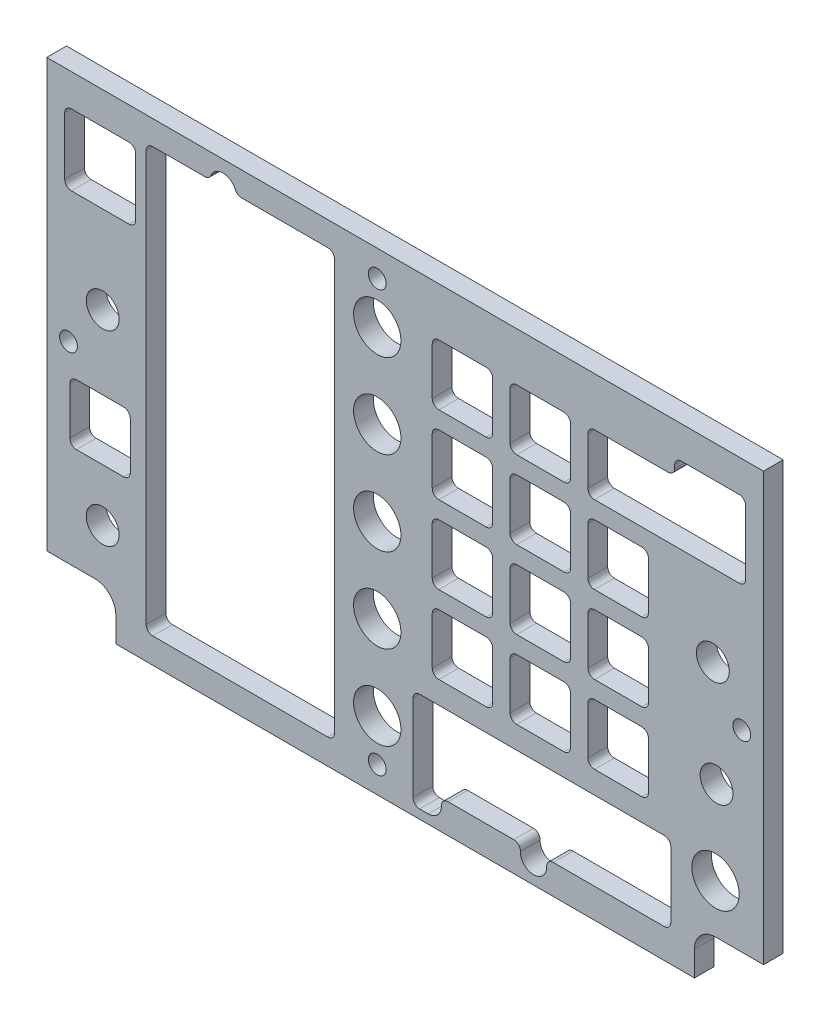
SolidWorks part; units mm, degrees
material "ABS PC"
ref_plane "Front Plane" through (0, 0, 0) normal (0, 0, 1) x (1, 0, 0)
ref_plane "Top Plane" through (0, 0, 0) normal (0, 1, 0) x (1, 0, 0)
ref_plane "Right Plane" through (0, 0, 0) normal (1, 0, 0) x (0, 0, -1)
sketch "Sketch1" plane through (0, 0, 0) normal (0, 0, 1) x (1, 0, 0)
  line L8 (74.93, -171.1167) -> (86.5187, -171.1167)
  line L9 (86.5187, -171.1167) -> (86.5187, -67.9292)
  line L10 (86.5187, -67.9292) -> (-86.5187, -67.9292)
  line L11 (-86.5187, -67.9292) -> (-86.5187, -171.1167)
  line L12 (-86.5187, -171.1167) -> (-74.93, -171.1167)
  line L13 (-69.85, -176.1967) -> (-69.85, -182.2292)
  line L14 (-69.85, -182.2292) -> (69.85, -182.2292)
  line L15 (69.85, -182.2292) -> (69.85, -176.1967)
  line L16 (74.93, -171.1167) -> (86.5187, -171.1167)
  line L17 (86.5187, -171.1167) -> (86.5187, -67.9292)
  line L18 (86.5187, -67.9292) -> (-86.5187, -67.9292)
  line L19 (-86.5187, -67.9292) -> (-86.5187, -171.1167)
  line L20 (-86.5187, -171.1167) -> (-74.93, -171.1167)
  line L21 (-69.85, -176.1967) -> (-69.85, -182.2292)
  line L22 (-69.85, -182.2292) -> (69.85, -182.2292)
  line L23 (69.85, -182.2292) -> (69.85, -176.1967)
  arc A2 (-69.85, -176.1967) -> (-74.93, -171.1167) centre (-74.93, -176.1967) ccw
  arc A3 (74.93, -171.1167) -> (69.85, -176.1967) centre (74.93, -176.1967) ccw
  arc A4 (-69.85, -176.1967) -> (-74.93, -171.1167) centre (-74.93, -176.1967) ccw
  arc A5 (74.93, -171.1167) -> (69.85, -176.1967) centre (74.93, -176.1967) ccw
  dimension "D1" = 0
extrude "Boss-Extrude1" add sketch "Sketch1" against normal blind 4.7625
sketch "Sketch3" plane through (0, 0, 0) normal (0, 0, 1) x (1, 0, 0)
  line L0 (-67.6275, -133.0167) -> (-79.6925, -133.0167) construction
  line L1 (-79.6925, -133.0167) -> (-79.6925, -145.0817) construction
  line L2 (-79.6925, -145.0817) -> (-67.6275, -145.0817) construction
  line L3 (-67.6275, -145.0817) -> (-67.6275, -133.0167) construction
  line L4 (19.8755, -149.3997) -> (19.8755, -137.3347) construction
  line L5 (19.8755, -137.3347) -> (7.8105, -137.3347) construction
  line L6 (7.8105, -137.3347) -> (7.8105, -149.3997) construction
  line L7 (7.8105, -149.3997) -> (19.8755, -149.3997) construction
  line L8 (38.6715, -149.3997) -> (38.6715, -137.3347) construction
  line L9 (38.6715, -137.3347) -> (26.6065, -137.3347) construction
  line L10 (26.6065, -137.3347) -> (26.6065, -149.3997) construction
  line L11 (26.6065, -149.3997) -> (38.6715, -149.3997) construction
  line L12 (45.4025, -149.3997) -> (57.4675, -149.3997) construction
  line L13 (57.4675, -149.3997) -> (57.4675, -137.3347) construction
  line L14 (57.4675, -137.3347) -> (45.4025, -137.3347) construction
  line L15 (45.4025, -137.3347) -> (45.4025, -149.3997) construction
  line L16 (57.4675, -130.6037) -> (57.4675, -118.5387) construction
  line L17 (57.4675, -118.5387) -> (45.4025, -118.5387) construction
  line L18 (45.4025, -118.5387) -> (45.4025, -130.6037) construction
  line L19 (45.4025, -130.6037) -> (57.4675, -130.6037) construction
  line L20 (38.6715, -130.6037) -> (38.6715, -118.5387) construction
  line L21 (38.6715, -118.5387) -> (26.6065, -118.5387) construction
  line L22 (26.6065, -118.5387) -> (26.6065, -130.6037) construction
  line L23 (26.6065, -130.6037) -> (38.6715, -130.6037) construction
  line L24 (19.8755, -130.6037) -> (19.8755, -118.5387) construction
  line L25 (19.8755, -118.5387) -> (7.8105, -118.5387) construction
  line L26 (7.8105, -118.5387) -> (7.8105, -130.6037) construction
  line L27 (7.8105, -130.6037) -> (19.8755, -130.6037) construction
  line L28 (19.8755, -111.8077) -> (19.8755, -99.7427) construction
  line L29 (19.8755, -99.7427) -> (7.8105, -99.7427) construction
  line L30 (7.8105, -99.7427) -> (7.8105, -111.8077) construction
  line L31 (7.8105, -111.8077) -> (19.8755, -111.8077) construction
  line L32 (19.8755, -93.0117) -> (19.8755, -80.9467) construction
  line L33 (19.8755, -80.9467) -> (7.8105, -80.9467) construction
  line L34 (7.8105, -80.9467) -> (7.8105, -93.0117) construction
  line L35 (7.8105, -93.0117) -> (19.8755, -93.0117) construction
  line L36 (38.6715, -93.0117) -> (38.6715, -80.9467) construction
  line L37 (38.6715, -80.9467) -> (26.6065, -80.9467) construction
  line L38 (26.6065, -80.9467) -> (26.6065, -93.0117) construction
  line L39 (26.6065, -93.0117) -> (38.6715, -93.0117) construction
  line L40 (38.6715, -111.8077) -> (38.6715, -99.7427) construction
  line L41 (38.6715, -99.7427) -> (26.6065, -99.7427) construction
  line L42 (26.6065, -99.7427) -> (26.6065, -111.8077) construction
  line L43 (26.6065, -111.8077) -> (38.6715, -111.8077) construction
  line L44 (57.4675, -111.8077) -> (57.4675, -99.7427) construction
  line L45 (57.4675, -99.7427) -> (45.4025, -99.7427) construction
  line L46 (45.4025, -99.7427) -> (45.4025, -111.8077) construction
  line L47 (45.4025, -111.8077) -> (57.4675, -111.8077) construction
  line L48 (57.4675, -93.0117) -> (57.4675, -80.9467) construction
  line L49 (57.4675, -80.9467) -> (45.4025, -80.9467) construction
  line L50 (45.4025, -80.9467) -> (45.4025, -93.0117) construction
  line L51 (45.4025, -93.0117) -> (57.4675, -93.0117) construction
  line L52 (-67.6275, -133.0167) -> (-79.6925, -133.0167)
  line L53 (-79.6925, -133.0167) -> (-79.6925, -145.0817)
  line L54 (-79.6925, -145.0817) -> (-67.6275, -145.0817)
  line L55 (-67.6275, -145.0817) -> (-67.6275, -133.0167)
  line L56 (19.8755, -149.3997) -> (19.8755, -137.3347)
  line L57 (19.8755, -137.3347) -> (7.8105, -137.3347)
  line L58 (7.8105, -137.3347) -> (7.8105, -149.3997)
  line L59 (7.8105, -149.3997) -> (19.8755, -149.3997)
  line L60 (38.6715, -149.3997) -> (38.6715, -137.3347)
  line L61 (38.6715, -137.3347) -> (26.6065, -137.3347)
  line L62 (26.6065, -137.3347) -> (26.6065, -149.3997)
  line L63 (26.6065, -149.3997) -> (38.6715, -149.3997)
  line L64 (45.4025, -149.3997) -> (57.4675, -149.3997)
  line L65 (57.4675, -149.3997) -> (57.4675, -137.3347)
  line L66 (57.4675, -137.3347) -> (45.4025, -137.3347)
  line L67 (45.4025, -137.3347) -> (45.4025, -149.3997)
  line L68 (57.4675, -130.6037) -> (57.4675, -118.5387)
  line L69 (57.4675, -118.5387) -> (45.4025, -118.5387)
  line L70 (45.4025, -118.5387) -> (45.4025, -130.6037)
  line L71 (45.4025, -130.6037) -> (57.4675, -130.6037)
  line L72 (38.6715, -130.6037) -> (38.6715, -118.5387)
  line L73 (38.6715, -118.5387) -> (26.6065, -118.5387)
  line L74 (26.6065, -118.5387) -> (26.6065, -130.6037)
  line L75 (26.6065, -130.6037) -> (38.6715, -130.6037)
  line L76 (19.8755, -130.6037) -> (19.8755, -118.5387)
  line L77 (19.8755, -118.5387) -> (7.8105, -118.5387)
  line L78 (7.8105, -118.5387) -> (7.8105, -130.6037)
  line L79 (7.8105, -130.6037) -> (19.8755, -130.6037)
  line L80 (19.8755, -111.8077) -> (19.8755, -99.7427)
  line L81 (19.8755, -99.7427) -> (7.8105, -99.7427)
  line L82 (7.8105, -99.7427) -> (7.8105, -111.8077)
  line L83 (7.8105, -111.8077) -> (19.8755, -111.8077)
  line L84 (19.8755, -93.0117) -> (19.8755, -80.9467)
  line L85 (19.8755, -80.9467) -> (7.8105, -80.9467)
  line L86 (7.8105, -80.9467) -> (7.8105, -93.0117)
  line L87 (7.8105, -93.0117) -> (19.8755, -93.0117)
  line L88 (38.6715, -93.0117) -> (38.6715, -80.9467)
  line L89 (38.6715, -80.9467) -> (26.6065, -80.9467)
  line L90 (26.6065, -80.9467) -> (26.6065, -93.0117)
  line L91 (26.6065, -93.0117) -> (38.6715, -93.0117)
  line L92 (38.6715, -111.8077) -> (38.6715, -99.7427)
  line L93 (38.6715, -99.7427) -> (26.6065, -99.7427)
  line L94 (26.6065, -99.7427) -> (26.6065, -111.8077)
  line L95 (26.6065, -111.8077) -> (38.6715, -111.8077)
  line L96 (57.4675, -111.8077) -> (57.4675, -99.7427)
  line L97 (57.4675, -99.7427) -> (45.4025, -99.7427)
  line L98 (45.4025, -99.7427) -> (45.4025, -111.8077)
  line L99 (45.4025, -111.8077) -> (57.4675, -111.8077)
  line L100 (57.4675, -93.0117) -> (57.4675, -80.9467)
  line L101 (57.4675, -80.9467) -> (45.4025, -80.9467)
  line L102 (45.4025, -80.9467) -> (45.4025, -93.0117)
  line L103 (45.4025, -93.0117) -> (57.4675, -93.0117)
  circle A0 centre (74.93, -159.3692) radius 4.445 construction
  circle A1 centre (-6.731, -165.7192) radius 4.445 construction
  circle A2 centre (-6.731, -145.3992) radius 4.445 construction
  circle A3 centre (-6.731, -125.0792) radius 4.445 construction
  circle A4 centre (-6.731, -104.7592) radius 4.445 construction
  circle A5 centre (-6.731, -84.4392) radius 4.445 construction
  circle A6 centre (74.93, -159.3692) radius 4.445
  circle A7 centre (-6.731, -165.7192) radius 4.445
  circle A8 centre (-6.731, -145.3992) radius 4.445
  circle A9 centre (-6.731, -125.0792) radius 4.445
  circle A10 centre (-6.731, -104.7592) radius 4.445
  circle A11 centre (-6.731, -84.4392) radius 4.445
extrude "Cut-Extrude1" [suppressed] cut sketch "Sketch3" against normal through all
sketch "Sketch4" plane through (0, 0, 0) normal (0, 0, 1) x (1, 0, 0)
  circle A0 centre (-73.025, -113.9667) radius 3.9688
  circle A1 centre (-73.025, -159.0517) radius 3.9688
  circle A2 centre (74.295, -113.9667) radius 3.9688
  circle A3 centre (75.184, -139.0492) radius 3.9687
  dimension "D1" = 7.9375
extrude "Cut-Extrude2" cut sketch "Sketch4" against normal through all
sketch "Sketch5" plane through (0, 0, 0) normal (0, 0, 1) x (1, 0, 0)
  line L0 (-79.63, -73.9922) -> (-79.63, -94.6322)
  line L1 (-79.63, -94.6322) -> (-67.69, -94.6322)
  line L2 (-67.69, -94.6322) -> (-67.69, -73.9922)
  line L3 (-67.69, -73.9922) -> (-79.63, -73.9922)
  line L4 (-78.36, -75.2622) -> (-78.36, -93.3622)
  line L5 (-78.36, -93.3622) -> (-68.96, -93.3622)
  line L6 (-68.96, -93.3622) -> (-68.96, -75.2622)
  line L7 (-68.96, -75.2622) -> (-78.36, -75.2622)
  line L8 (-78.36, -75.2622) -> (-78.36, -93.3622) construction
  line L9 (-78.36, -93.3622) -> (-68.96, -93.3622) construction
  line L10 (-68.96, -93.3622) -> (-68.96, -75.2622) construction
  line L11 (-68.96, -75.2622) -> (-78.36, -75.2622) construction
  line L12 (68.96, -75.2622) -> (68.96, -93.3622)
  line L13 (68.96, -93.3622) -> (78.36, -93.3622)
  line L14 (78.36, -93.3622) -> (78.36, -75.2622)
  line L15 (78.36, -75.2622) -> (68.96, -75.2622)
  line L16 (68.96, -75.2622) -> (68.96, -93.3622) construction
  line L17 (68.96, -93.3622) -> (78.36, -93.3622) construction
  line L18 (78.36, -93.3622) -> (78.36, -75.2622) construction
  line L19 (78.36, -75.2622) -> (68.96, -75.2622) construction
  line L20 (67.69, -73.9922) -> (67.69, -94.6322)
  line L21 (67.69, -94.6322) -> (79.63, -94.6322)
  line L22 (79.63, -94.6322) -> (79.63, -73.9922)
  line L23 (79.63, -73.9922) -> (67.69, -73.9922)
  line L24 (-61.06, -75.0622) -> (-51.66, -75.0622) construction
  line L25 (-62.53, -73.7922) -> (-17.068, -73.7922)
  line L26 (-62.53, -73.7922) -> (-62.53, -176.1122)
  line L27 (-62.53, -176.1122) -> (-17.068, -176.1122)
  line L28 (-17.068, -73.7922) -> (-17.068, -176.1122)
  line L29 (-62.53, -73.7922) -> (-17.068, -176.1122) construction
  line L30 (-62.53, -176.1122) -> (-17.068, -73.7922) construction
  line L31 (-61.26, -93.3622) -> (-61.26, -75.2622) construction
  line L32 (-51.66, -174.8422) -> (-61.06, -174.8422) construction
  line L33 (-18.338, -167.7344) -> (-18.338, -169.4031) construction
  line L34 (61.52, -158.4422) -> (61.52, -172.5422) construction
  line L35 (5.02, -157.9422) -> (61.02, -157.9422) construction
  line L36 (61.02, -173.0422) -> (5.02, -173.0422) construction
  line L37 (4.52, -172.5422) -> (4.52, -158.4422) construction
  line L38 (61.52, -157.9422) -> (61.52, -173.0422)
  line L39 (4.52, -157.9422) -> (61.52, -157.9422)
  line L40 (61.52, -173.0422) -> (4.52, -173.0422)
  line L41 (4.52, -173.0422) -> (4.52, -157.9422)
  point P20 (-39.799, -124.9522)
  dimension "D4" = 1.27
  dimension "D5" = 1.27
  dimension "D6" = 1.27
  dimension "D7" = 1.27
  dimension "D1" = 0
  dimension "D2" = 0
  dimension "D3" = 1.27
extrude "Cut-Extrude3" [suppressed] cut sketch "Sketch5" against normal through all
sketch "Sketch6" plane through (0, 0, 0) normal (0, 0, 1) x (1, 0, 0)
  line L4 (-67.6275, -133.0167) -> (-79.6925, -133.0167) construction
  line L5 (57.4675, -137.3347) -> (45.4025, -137.3347) construction
  line L6 (45.4025, -137.3347) -> (45.4025, -149.3997) construction
  line L7 (45.4025, -149.3997) -> (57.4675, -149.3997) construction
  line L8 (57.4675, -149.3997) -> (57.4675, -137.3347) construction
  line L9 (45.4025, -130.6037) -> (57.4675, -130.6037) construction
  line L10 (57.4675, -130.6037) -> (57.4675, -118.5387) construction
  line L11 (57.4675, -118.5387) -> (45.4025, -118.5387) construction
  line L12 (45.4025, -118.5387) -> (45.4025, -130.6037) construction
  line L13 (45.4025, -111.8077) -> (57.4675, -111.8077) construction
  line L14 (57.4675, -111.8077) -> (57.4675, -99.7427) construction
  line L15 (57.4675, -99.7427) -> (45.4025, -99.7427) construction
  line L16 (45.4025, -99.7427) -> (45.4025, -111.8077) construction
  line L17 (45.4025, -93.0117) -> (57.4675, -93.0117) construction
  line L18 (57.4675, -93.0117) -> (57.4675, -80.9467) construction
  line L19 (57.4675, -80.9467) -> (45.4025, -80.9467) construction
  line L20 (45.4025, -80.9467) -> (45.4025, -93.0117) construction
  line L21 (26.6065, -149.3997) -> (38.6715, -149.3997) construction
  line L22 (38.6715, -149.3997) -> (38.6715, -137.3347) construction
  line L23 (38.6715, -137.3347) -> (26.6065, -137.3347) construction
  line L24 (26.6065, -137.3347) -> (26.6065, -149.3997) construction
  line L25 (26.6065, -130.6037) -> (38.6715, -130.6037) construction
  line L26 (38.6715, -130.6037) -> (38.6715, -118.5387) construction
  line L27 (38.6715, -118.5387) -> (26.6065, -118.5387) construction
  line L28 (26.6065, -118.5387) -> (26.6065, -130.6037) construction
  line L29 (26.6065, -111.8077) -> (38.6715, -111.8077) construction
  line L30 (38.6715, -111.8077) -> (38.6715, -99.7427) construction
  line L31 (38.6715, -99.7427) -> (26.6065, -99.7427) construction
  line L32 (26.6065, -99.7427) -> (26.6065, -111.8077) construction
  line L33 (26.6065, -93.0117) -> (38.6715, -93.0117) construction
  line L34 (38.6715, -93.0117) -> (38.6715, -80.9467) construction
  line L35 (38.6715, -80.9467) -> (26.6065, -80.9467) construction
  line L36 (26.6065, -80.9467) -> (26.6065, -93.0117) construction
  line L37 (7.8105, -93.0117) -> (19.8755, -93.0117) construction
  line L38 (19.8755, -93.0117) -> (19.8755, -80.9467) construction
  line L39 (19.8755, -80.9467) -> (7.8105, -80.9467) construction
  line L40 (7.8105, -80.9467) -> (7.8105, -93.0117) construction
  line L41 (7.8105, -111.8077) -> (19.8755, -111.8077) construction
  line L42 (19.8755, -111.8077) -> (19.8755, -99.7427) construction
  line L43 (19.8755, -99.7427) -> (7.8105, -99.7427) construction
  line L44 (7.8105, -99.7427) -> (7.8105, -111.8077) construction
  line L45 (19.8755, -118.5387) -> (7.8105, -118.5387) construction
  line L46 (7.8105, -118.5387) -> (7.8105, -130.6037) construction
  line L47 (7.8105, -130.6037) -> (19.8755, -130.6037) construction
  line L48 (19.8755, -130.6037) -> (19.8755, -118.5387) construction
  line L49 (19.8755, -137.3347) -> (7.8105, -137.3347) construction
  line L50 (7.8105, -137.3347) -> (7.8105, -149.3997) construction
  line L51 (7.8105, -149.3997) -> (19.8755, -149.3997) construction
  line L52 (19.8755, -149.3997) -> (19.8755, -137.3347) construction
  line L53 (-79.6925, -133.0167) -> (-79.6925, -145.0817) construction
  line L54 (-79.6925, -145.0817) -> (-67.6275, -145.0817) construction
  line L55 (-67.6275, -145.0817) -> (-67.6275, -133.0167) construction
  line L56 (57.4675, -137.3347) -> (45.4025, -137.3347) construction
  line L57 (45.4025, -137.3347) -> (45.4025, -149.3997) construction
  line L58 (45.4025, -149.3997) -> (57.4675, -149.3997) construction
  line L59 (57.4675, -149.3997) -> (57.4675, -137.3347) construction
  line L60 (45.4025, -130.6037) -> (57.4675, -130.6037) construction
  line L61 (57.4675, -130.6037) -> (57.4675, -118.5387) construction
  line L62 (57.4675, -118.5387) -> (45.4025, -118.5387) construction
  line L63 (45.4025, -118.5387) -> (45.4025, -130.6037) construction
  line L64 (45.4025, -111.8077) -> (57.4675, -111.8077) construction
  line L65 (57.4675, -111.8077) -> (57.4675, -99.7427) construction
  line L66 (57.4675, -99.7427) -> (45.4025, -99.7427) construction
  line L67 (45.4025, -99.7427) -> (45.4025, -111.8077) construction
  line L68 (45.4025, -93.0117) -> (57.4675, -93.0117) construction
  line L69 (57.4675, -93.0117) -> (57.4675, -80.9467) construction
  line L70 (57.4675, -80.9467) -> (45.4025, -80.9467) construction
  line L71 (45.4025, -80.9467) -> (45.4025, -93.0117) construction
  line L72 (26.6065, -149.3997) -> (38.6715, -149.3997) construction
  line L73 (38.6715, -149.3997) -> (38.6715, -137.3347) construction
  line L74 (38.6715, -137.3347) -> (26.6065, -137.3347) construction
  line L75 (26.6065, -137.3347) -> (26.6065, -149.3997) construction
  line L76 (26.6065, -130.6037) -> (38.6715, -130.6037) construction
  line L77 (38.6715, -130.6037) -> (38.6715, -118.5387) construction
  line L78 (38.6715, -118.5387) -> (26.6065, -118.5387) construction
  line L79 (26.6065, -118.5387) -> (26.6065, -130.6037) construction
  line L80 (26.6065, -111.8077) -> (38.6715, -111.8077) construction
  line L81 (38.6715, -111.8077) -> (38.6715, -99.7427) construction
  line L82 (38.6715, -99.7427) -> (26.6065, -99.7427) construction
  line L83 (26.6065, -99.7427) -> (26.6065, -111.8077) construction
  line L84 (26.6065, -93.0117) -> (38.6715, -93.0117) construction
  line L85 (38.6715, -93.0117) -> (38.6715, -80.9467) construction
  line L86 (38.6715, -80.9467) -> (26.6065, -80.9467) construction
  line L87 (26.6065, -80.9467) -> (26.6065, -93.0117) construction
  line L88 (7.8105, -93.0117) -> (19.8755, -93.0117) construction
  line L89 (19.8755, -93.0117) -> (19.8755, -80.9467) construction
  line L90 (19.8755, -80.9467) -> (7.8105, -80.9467) construction
  line L91 (7.8105, -80.9467) -> (7.8105, -93.0117) construction
  line L92 (7.8105, -111.8077) -> (19.8755, -111.8077) construction
  line L93 (19.8755, -111.8077) -> (19.8755, -99.7427) construction
  line L94 (19.8755, -99.7427) -> (7.8105, -99.7427) construction
  line L95 (7.8105, -99.7427) -> (7.8105, -111.8077) construction
  line L96 (19.8755, -118.5387) -> (7.8105, -118.5387) construction
  line L97 (7.8105, -118.5387) -> (7.8105, -130.6037) construction
  line L98 (7.8105, -130.6037) -> (19.8755, -130.6037) construction
  line L99 (19.8755, -130.6037) -> (19.8755, -118.5387) construction
  line L100 (19.8755, -137.3347) -> (7.8105, -137.3347) construction
  line L101 (7.8105, -137.3347) -> (7.8105, -149.3997) construction
  line L102 (7.8105, -149.3997) -> (19.8755, -149.3997) construction
  line L103 (19.8755, -149.3997) -> (19.8755, -137.3347) construction
  line L104 (-67.6275, -133.0167) -> (-79.6925, -133.0167) construction
  line L105 (-79.6925, -133.0167) -> (-79.6925, -145.0817) construction
  line L106 (-79.6925, -145.0817) -> (-67.6275, -145.0817) construction
  line L107 (-67.6275, -145.0817) -> (-67.6275, -133.0167) construction
  line L108 (58.7375, -136.0647) -> (44.1325, -136.0647)
  line L109 (44.1325, -136.0647) -> (44.1325, -150.6697)
  line L110 (44.1325, -150.6697) -> (58.7375, -150.6697)
  line L111 (58.7375, -150.6697) -> (58.7375, -136.0647)
  line L112 (44.1325, -131.8737) -> (58.7375, -131.8737)
  line L113 (58.7375, -131.8737) -> (58.7375, -117.2687)
  line L114 (58.7375, -117.2687) -> (44.1325, -117.2687)
  line L115 (44.1325, -117.2687) -> (44.1325, -131.8737)
  line L116 (44.1325, -113.0777) -> (58.7375, -113.0777)
  line L117 (58.7375, -113.0777) -> (58.7375, -98.4727)
  line L118 (58.7375, -98.4727) -> (44.1325, -98.4727)
  line L119 (44.1325, -98.4727) -> (44.1325, -113.0777)
  line L120 (44.1325, -94.2817) -> (58.7375, -94.2817)
  line L121 (58.7375, -94.2817) -> (58.7375, -79.6767)
  line L122 (58.7375, -79.6767) -> (44.1325, -79.6767)
  line L123 (44.1325, -79.6767) -> (44.1325, -94.2817)
  line L124 (25.3365, -150.6697) -> (39.9415, -150.6697)
  line L125 (39.9415, -150.6697) -> (39.9415, -136.0647)
  line L126 (39.9415, -136.0647) -> (25.3365, -136.0647)
  line L127 (25.3365, -136.0647) -> (25.3365, -150.6697)
  line L128 (25.3365, -131.8737) -> (39.9415, -131.8737)
  line L129 (39.9415, -131.8737) -> (39.9415, -117.2687)
  line L130 (39.9415, -117.2687) -> (25.3365, -117.2687)
  line L131 (25.3365, -117.2687) -> (25.3365, -131.8737)
  line L132 (25.3365, -113.0777) -> (39.9415, -113.0777)
  line L133 (39.9415, -113.0777) -> (39.9415, -98.4727)
  line L134 (39.9415, -98.4727) -> (25.3365, -98.4727)
  line L135 (25.3365, -98.4727) -> (25.3365, -113.0777)
  line L136 (25.3365, -94.2817) -> (39.9415, -94.2817)
  line L137 (39.9415, -94.2817) -> (39.9415, -79.6767)
  line L138 (39.9415, -79.6767) -> (25.3365, -79.6767)
  line L139 (25.3365, -79.6767) -> (25.3365, -94.2817)
  line L140 (6.5405, -94.2817) -> (21.1455, -94.2817)
  line L141 (21.1455, -94.2817) -> (21.1455, -79.6767)
  line L142 (21.1455, -79.6767) -> (6.5405, -79.6767)
  line L143 (6.5405, -79.6767) -> (6.5405, -94.2817)
  line L144 (6.5405, -113.0777) -> (21.1455, -113.0777)
  line L145 (21.1455, -113.0777) -> (21.1455, -98.4727)
  line L146 (21.1455, -98.4727) -> (6.5405, -98.4727)
  line L147 (6.5405, -98.4727) -> (6.5405, -113.0777)
  line L148 (21.1455, -117.2687) -> (6.5405, -117.2687)
  line L149 (6.5405, -117.2687) -> (6.5405, -131.8737)
  line L150 (6.5405, -131.8737) -> (21.1455, -131.8737)
  line L151 (21.1455, -131.8737) -> (21.1455, -117.2687)
  line L152 (21.1455, -136.0647) -> (6.5405, -136.0647)
  line L153 (6.5405, -136.0647) -> (6.5405, -150.6697)
  line L154 (6.5405, -150.6697) -> (21.1455, -150.6697)
  line L155 (21.1455, -150.6697) -> (21.1455, -136.0647)
  line L156 (-66.3575, -131.7467) -> (-80.9625, -131.7467)
  line L157 (-80.9625, -131.7467) -> (-80.9625, -146.3517)
  line L158 (-80.9625, -146.3517) -> (-66.3575, -146.3517)
  line L159 (-66.3575, -146.3517) -> (-66.3575, -131.7467)
  circle A6 centre (74.93, -159.3692) radius 4.445 construction
  circle A7 centre (-6.731, -165.7192) radius 4.445 construction
  circle A9 centre (-6.731, -145.3992) radius 4.445 construction
  circle A12 centre (-6.731, -125.0792) radius 4.445 construction
  circle A16 centre (-6.731, -104.7592) radius 4.445 construction
  circle A21 centre (-6.731, -84.4392) radius 4.445 construction
  circle A33 centre (74.93, -159.3692) radius 4.445 construction
  circle A34 centre (-6.731, -165.7192) radius 4.445 construction
  circle A35 centre (-6.731, -145.3992) radius 4.445 construction
  circle A36 centre (-6.731, -125.0792) radius 4.445 construction
  circle A37 centre (-6.731, -104.7592) radius 4.445 construction
  circle A38 centre (-6.731, -84.4392) radius 4.445 construction
  circle A39 centre (74.93, -159.3692) radius 5.715
  circle A40 centre (-6.731, -165.7192) radius 5.715
  circle A41 centre (-6.731, -145.3992) radius 5.715
  circle A42 centre (-6.731, -125.0792) radius 5.715
  circle A43 centre (-6.731, -104.7592) radius 5.715
  circle A44 centre (-6.731, -84.4392) radius 5.715
  dimension "D1" = 1.27
extrude "Cut-Extrude4" [suppressed] cut sketch "Sketch6" against normal through all
sketch "Sketch7" plane through (0, 0, 0) normal (0, 0, 1) x (1, 0, 0)
  line L0 (66.04, -176.9122) -> (66.04, -148.2722)
  line L1 (66.04, -148.2722) -> (0, -148.2722)
  line L2 (0, -148.2722) -> (0, -176.9122)
  line L3 (0, -176.9122) -> (66.04, -176.9122)
  line L4 (64.77, -175.6422) -> (64.77, -149.5422)
  line L5 (64.77, -149.5422) -> (1.27, -149.5422)
  line L6 (1.27, -149.5422) -> (1.27, -175.6422)
  line L7 (1.27, -175.6422) -> (64.77, -175.6422)
  line L8 (64.77, -175.6422) -> (64.77, -149.5422) construction
  line L9 (64.77, -149.5422) -> (1.27, -149.5422) construction
  line L10 (1.27, -149.5422) -> (1.27, -175.6422) construction
  line L11 (1.27, -175.6422) -> (64.77, -175.6422) construction
  dimension "D1" = 0
  dimension "D2" = 1.27
extrude "Cut-Extrude5" [suppressed] cut sketch "Sketch7" against normal through all
hole_wizard "#6 Clearance Hole2" positions "Sketch10" profile "Sketch11" hole size "#6" standard "ANSI Inch" end condition through all
sketch "Sketch10" plane through (0, 0, 1.5875) normal (0, 0, 1) x (-1, 0, 0)
  point P0 (-81.28, 124.6982)
  point P3 (6.731, 175.8792)
  point P6 (81.28, 124.6982)
  point P9 (6.731, 74.2792)
sketch "Sketch11" plane through (81.28, -124.6982, 1.5875) normal (1, 0, 0) x (0, -1, 0)
  line L0 (0, 0) -> (0, 6.35)
  line L1 (0, 6.35) -> (2.1526, 6.35)
  line L2 (2.1526, 6.35) -> (2.1526, 0)
  line L3 (2.1526, 0) -> (0, 0)
  line L4 (0, -6.35) -> (0, 107.95) construction
  dimension "Thru Hole Dia." = 4.3053
  dimension "Thru Hole Depth" = 6.35
sketch "Sketch12" plane through (0, 0, -4.7625) normal (0, 0, -1) x (-1, 0, 0)
  line L0 (73.6125, -76.7792) -> (73.6125, -91.7792) construction
  line L1 (-73.6482, -76.8365) -> (-73.6482, -91.8365) construction
  line L4 (66.1125, -76.7792) -> (66.1125, -91.7792)
  line L5 (81.1125, -76.7792) -> (66.1125, -76.7792)
  line L6 (66.1125, -91.7792) -> (81.1125, -91.7792)
  line L7 (81.1125, -91.7792) -> (81.1125, -76.7792)
  line L10 (-81.1482, -76.8365) -> (-81.1482, -91.8365)
  line L11 (-66.1482, -91.8365) -> (-66.1482, -76.8365)
  line L12 (-66.1482, -91.8365) -> (-81.1482, -91.8365)
  line L13 (-81.1482, -76.8365) -> (-66.1482, -76.8365)
  point P12 (-73.6482, -84.3365)
  point P13 (73.6125, -84.2792)
  dimension "D1" = 15
extrude "Cut-Extrude6" [suppressed] cut sketch "Sketch12" against normal up to next
sketch "Sketch15" plane through (0, 0, -4.7625) normal (0, 0, -1) x (-1, 0, 0)
  line L4 (-58.7375, -137.6522) -> (-58.7375, -149.0822)
  line L5 (-45.72, -136.0647) -> (-57.15, -136.0647)
  line L6 (-44.1325, -149.0822) -> (-44.1325, -137.6522)
  line L7 (-57.15, -150.6697) -> (-45.72, -150.6697)
  line L8 (-58.7375, -137.6522) -> (-58.7375, -149.0822)
  line L9 (-45.72, -136.0647) -> (-57.15, -136.0647)
  line L10 (-44.1325, -149.0822) -> (-44.1325, -137.6522)
  line L11 (-57.15, -150.6697) -> (-45.72, -150.6697)
  line L12 (-58.7375, -118.8562) -> (-58.7375, -130.2862)
  line L13 (-45.72, -117.2687) -> (-57.15, -117.2687)
  line L14 (-44.1325, -130.2862) -> (-44.1325, -118.8562)
  line L15 (-57.15, -131.8737) -> (-45.72, -131.8737)
  line L16 (-58.7375, -118.8562) -> (-58.7375, -130.2862)
  line L17 (-45.72, -117.2687) -> (-57.15, -117.2687)
  line L18 (-44.1325, -130.2862) -> (-44.1325, -118.8562)
  line L19 (-57.15, -131.8737) -> (-45.72, -131.8737)
  line L20 (-58.7375, -100.0602) -> (-58.7375, -111.4902)
  line L21 (-45.72, -98.4727) -> (-57.15, -98.4727)
  line L22 (-44.1325, -111.4902) -> (-44.1325, -100.0602)
  line L23 (-57.15, -113.0777) -> (-45.72, -113.0777)
  line L24 (-58.7375, -100.0602) -> (-58.7375, -111.4902)
  line L25 (-45.72, -98.4727) -> (-57.15, -98.4727)
  line L26 (-44.1325, -111.4902) -> (-44.1325, -100.0602)
  line L27 (-57.15, -113.0777) -> (-45.72, -113.0777)
  line L28 (-39.9415, -81.2642) -> (-39.9415, -92.6942)
  line L29 (-45.72, -79.6767) -> (-63.4882, -79.6767)
  line L30 (-44.1325, -92.6942) -> (-44.1325, -81.2642)
  line L31 (-80.6332, -94.2817) -> (-45.72, -94.2817)
  line L32 (-82.2207, -77.3272) -> (-82.2207, -92.6942)
  line L33 (-66.6632, -75.7397) -> (-80.6332, -75.7397)
  line L34 (-45.72, -79.6767) -> (-63.4882, -79.6767)
  line L35 (-44.1325, -92.6942) -> (-44.1325, -81.2642)
  line L36 (-80.6332, -94.2817) -> (-45.72, -94.2817)
  line L37 (-82.2207, -77.3272) -> (-82.2207, -92.6942)
  line L38 (-66.6632, -75.7397) -> (-80.6332, -75.7397)
  line L39 (-26.924, -79.6767) -> (-38.354, -79.6767)
  line L40 (-25.3365, -92.6942) -> (-25.3365, -81.2642)
  line L41 (-38.354, -94.2817) -> (-26.924, -94.2817)
  line L42 (-39.9415, -81.2642) -> (-39.9415, -92.6942)
  line L43 (-26.924, -79.6767) -> (-38.354, -79.6767)
  line L44 (-25.3365, -92.6942) -> (-25.3365, -81.2642)
  line L45 (-38.354, -94.2817) -> (-26.924, -94.2817)
  line L46 (-39.9415, -100.0602) -> (-39.9415, -111.4902)
  line L47 (-26.924, -98.4727) -> (-38.354, -98.4727)
  line L48 (-25.3365, -111.4902) -> (-25.3365, -100.0602)
  line L49 (-38.354, -113.0777) -> (-26.924, -113.0777)
  line L50 (-39.9415, -100.0602) -> (-39.9415, -111.4902)
  line L51 (-26.924, -98.4727) -> (-38.354, -98.4727)
  line L52 (-25.3365, -111.4902) -> (-25.3365, -100.0602)
  line L53 (-38.354, -113.0777) -> (-26.924, -113.0777)
  line L54 (-39.9415, -118.8562) -> (-39.9415, -130.2862)
  line L55 (-26.924, -117.2687) -> (-38.354, -117.2687)
  line L56 (-25.3365, -130.2862) -> (-25.3365, -118.8562)
  line L57 (-38.354, -131.8737) -> (-26.924, -131.8737)
  line L58 (-39.9415, -118.8562) -> (-39.9415, -130.2862)
  line L59 (-26.924, -117.2687) -> (-38.354, -117.2687)
  line L60 (-25.3365, -130.2862) -> (-25.3365, -118.8562)
  line L61 (-38.354, -131.8737) -> (-26.924, -131.8737)
  line L62 (-39.9415, -137.6522) -> (-39.9415, -149.0822)
  line L63 (-26.924, -136.0647) -> (-38.354, -136.0647)
  line L64 (-25.3365, -149.0822) -> (-25.3365, -137.6522)
  line L65 (-38.354, -150.6697) -> (-26.924, -150.6697)
  line L66 (-39.9415, -137.6522) -> (-39.9415, -149.0822)
  line L67 (-26.924, -136.0647) -> (-38.354, -136.0647)
  line L68 (-25.3365, -149.0822) -> (-25.3365, -137.6522)
  line L69 (-38.354, -150.6697) -> (-26.924, -150.6697)
  line L70 (-6.5405, -149.0822) -> (-6.5405, -137.6522)
  line L71 (-19.558, -150.6697) -> (-8.128, -150.6697)
  line L72 (-26.2305, -175.1172) -> (-10.3495, -175.1172)
  line L73 (-62.5475, -175.1172) -> (-35.7495, -175.1172)
  line L74 (-64.135, -157.6547) -> (-64.135, -173.5297)
  line L75 (-3.4925, -156.0672) -> (-62.5475, -156.0672)
  line L76 (-1.905, -178.4617) -> (-1.905, -157.6547)
  line L77 (-5.59, -180.0492) -> (-3.4925, -180.0492)
  line L78 (-26.2305, -175.1172) -> (-10.3495, -175.1172)
  line L79 (-62.5475, -175.1172) -> (-35.7495, -175.1172)
  line L80 (-64.135, -157.6547) -> (-64.135, -173.5297)
  line L81 (-3.4925, -156.0672) -> (-62.5475, -156.0672)
  line L82 (-1.905, -178.4617) -> (-1.905, -157.6547)
  line L83 (-5.59, -180.0492) -> (-3.4925, -180.0492)
  line L84 (-21.1455, -137.6522) -> (-21.1455, -149.0822)
  line L85 (-8.128, -136.0647) -> (-19.558, -136.0647)
  line L86 (-6.5405, -149.0822) -> (-6.5405, -137.6522)
  line L87 (-19.558, -150.6697) -> (-8.128, -150.6697)
  line L88 (-21.1455, -137.6522) -> (-21.1455, -149.0822)
  line L89 (-8.128, -136.0647) -> (-19.558, -136.0647)
  line L90 (-6.5405, -130.2862) -> (-6.5405, -118.8562)
  line L91 (-19.558, -131.8737) -> (-8.128, -131.8737)
  line L92 (-21.1455, -118.8562) -> (-21.1455, -130.2862)
  line L93 (-8.128, -117.2687) -> (-19.558, -117.2687)
  line L94 (-6.5405, -130.2862) -> (-6.5405, -118.8562)
  line L95 (-19.558, -131.8737) -> (-8.128, -131.8737)
  line L96 (-21.1455, -118.8562) -> (-21.1455, -130.2862)
  line L97 (-8.128, -117.2687) -> (-19.558, -117.2687)
  line L98 (-21.1455, -100.0602) -> (-21.1455, -111.4902)
  line L99 (-8.128, -98.4727) -> (-19.558, -98.4727)
  line L100 (-6.5405, -111.4902) -> (-6.5405, -100.0602)
  line L101 (-19.558, -113.0777) -> (-8.128, -113.0777)
  line L102 (-21.1455, -100.0602) -> (-21.1455, -111.4902)
  line L103 (-8.128, -98.4727) -> (-19.558, -98.4727)
  line L104 (-6.5405, -111.4902) -> (-6.5405, -100.0602)
  line L105 (-19.558, -113.0777) -> (-8.128, -113.0777)
  line L106 (-21.1455, -81.2642) -> (-21.1455, -92.6942)
  line L107 (-8.128, -79.6767) -> (-19.558, -79.6767)
  line L108 (-6.5405, -92.6942) -> (-6.5405, -81.2642)
  line L109 (-19.558, -94.2817) -> (-8.128, -94.2817)
  line L110 (-21.1455, -81.2642) -> (-21.1455, -92.6942)
  line L111 (-8.128, -79.6767) -> (-19.558, -79.6767)
  line L112 (-6.5405, -92.6942) -> (-6.5405, -81.2642)
  line L113 (-19.558, -94.2817) -> (-8.128, -94.2817)
  line L114 (65.04, -77.3107) -> (65.04, -91.2807)
  line L115 (39.5306, -73.7922) -> (18.6555, -73.7922)
  line L116 (60.9425, -73.7922) -> (48.3494, -73.7922)
  line L117 (62.53, -174.5247) -> (62.53, -75.3797)
  line L118 (18.6555, -176.1122) -> (60.9425, -176.1122)
  line L119 (17.068, -75.3797) -> (17.068, -174.5247)
  line L120 (39.5306, -73.7922) -> (18.6555, -73.7922)
  line L121 (60.9425, -73.7922) -> (48.3494, -73.7922)
  line L122 (62.53, -174.5247) -> (62.53, -75.3797)
  line L123 (18.6555, -176.1122) -> (60.9425, -176.1122)
  line L124 (17.068, -75.3797) -> (17.068, -174.5247)
  line L125 (80.5975, -75.7232) -> (66.6275, -75.7232)
  line L126 (82.185, -91.2807) -> (82.185, -77.3107)
  line L127 (66.6275, -92.8682) -> (80.5975, -92.8682)
  line L128 (65.04, -77.3107) -> (65.04, -91.2807)
  line L129 (80.5975, -75.7232) -> (66.6275, -75.7232)
  line L130 (82.185, -91.2807) -> (82.185, -77.3107)
  line L131 (66.6275, -92.8682) -> (80.5975, -92.8682)
  line L132 (80.9625, -144.7642) -> (80.9625, -133.3342)
  line L133 (67.945, -146.3517) -> (79.375, -146.3517)
  line L134 (66.3575, -133.3342) -> (66.3575, -144.7642)
  line L135 (79.375, -131.7467) -> (67.945, -131.7467)
  line L136 (80.9625, -144.7642) -> (80.9625, -133.3342)
  line L137 (67.945, -146.3517) -> (79.375, -146.3517)
  line L138 (66.3575, -133.3342) -> (66.3575, -144.7642)
  line L139 (79.375, -131.7467) -> (67.945, -131.7467)
  line L146 (-65.0757, -78.0892) -> (-65.0757, -77.3272)
  line L147 (-65.0757, -78.0892) -> (-65.0757, -77.3272)
  circle A1 centre (-74.93, -159.3692) radius 5.715
  circle A2 centre (-74.93, -159.3692) radius 5.715
  circle A3 centre (6.731, -84.4392) radius 5.715
  circle A4 centre (6.731, -84.4392) radius 5.715
  circle A5 centre (6.731, -104.7592) radius 5.715
  arc A6 (-57.15, -136.0647) -> (-58.7375, -137.6522) centre (-57.15, -137.6522) ccw
  arc A7 (-44.1325, -137.6522) -> (-45.72, -136.0647) centre (-45.72, -137.6522) ccw
  arc A8 (-45.72, -150.6697) -> (-44.1325, -149.0822) centre (-45.72, -149.0822) ccw
  arc A9 (-58.7375, -149.0822) -> (-57.15, -150.6697) centre (-57.15, -149.0822) ccw
  arc A10 (-57.15, -136.0647) -> (-58.7375, -137.6522) centre (-57.15, -137.6522) ccw
  arc A11 (-44.1325, -137.6522) -> (-45.72, -136.0647) centre (-45.72, -137.6522) ccw
  arc A12 (-45.72, -150.6697) -> (-44.1325, -149.0822) centre (-45.72, -149.0822) ccw
  arc A13 (-58.7375, -149.0822) -> (-57.15, -150.6697) centre (-57.15, -149.0822) ccw
  arc A14 (-57.15, -117.2687) -> (-58.7375, -118.8562) centre (-57.15, -118.8562) ccw
  arc A15 (-44.1325, -118.8562) -> (-45.72, -117.2687) centre (-45.72, -118.8562) ccw
  arc A16 (-45.72, -131.8737) -> (-44.1325, -130.2862) centre (-45.72, -130.2862) ccw
  arc A17 (-58.7375, -130.2862) -> (-57.15, -131.8737) centre (-57.15, -130.2862) ccw
  arc A18 (-57.15, -117.2687) -> (-58.7375, -118.8562) centre (-57.15, -118.8562) ccw
  arc A19 (-44.1325, -118.8562) -> (-45.72, -117.2687) centre (-45.72, -118.8562) ccw
  arc A20 (-45.72, -131.8737) -> (-44.1325, -130.2862) centre (-45.72, -130.2862) ccw
  arc A21 (-58.7375, -130.2862) -> (-57.15, -131.8737) centre (-57.15, -130.2862) ccw
  arc A22 (-57.15, -98.4727) -> (-58.7375, -100.0602) centre (-57.15, -100.0602) ccw
  arc A23 (-44.1325, -100.0602) -> (-45.72, -98.4727) centre (-45.72, -100.0602) ccw
  arc A24 (-45.72, -113.0777) -> (-44.1325, -111.4902) centre (-45.72, -111.4902) ccw
  arc A25 (-58.7375, -111.4902) -> (-57.15, -113.0777) centre (-57.15, -111.4902) ccw
  arc A26 (-57.15, -98.4727) -> (-58.7375, -100.0602) centre (-57.15, -100.0602) ccw
  arc A27 (-44.1325, -100.0602) -> (-45.72, -98.4727) centre (-45.72, -100.0602) ccw
  arc A28 (-45.72, -113.0777) -> (-44.1325, -111.4902) centre (-45.72, -111.4902) ccw
  arc A29 (-58.7375, -111.4902) -> (-57.15, -113.0777) centre (-57.15, -111.4902) ccw
  arc A30 (-38.354, -79.6767) -> (-39.9415, -81.2642) centre (-38.354, -81.2642) ccw
  arc A31 (-25.3365, -81.2642) -> (-26.924, -79.6767) centre (-26.924, -81.2642) ccw
  arc A32 (-65.0757, -77.3272) -> (-66.6632, -75.7397) centre (-66.6632, -77.3272) ccw
  arc A33 (-65.0757, -78.0892) -> (-63.4882, -79.6767) centre (-63.4882, -78.0892) ccw
  arc A34 (-44.1325, -81.2642) -> (-45.72, -79.6767) centre (-45.72, -81.2642) ccw
  arc A35 (-45.72, -94.2817) -> (-44.1325, -92.6942) centre (-45.72, -92.6942) ccw
  arc A36 (-82.2207, -92.6942) -> (-80.6332, -94.2817) centre (-80.6332, -92.6942) ccw
  arc A37 (-80.6332, -75.7397) -> (-82.2207, -77.3272) centre (-80.6332, -77.3272) ccw
  arc A38 (-65.0757, -77.3272) -> (-66.6632, -75.7397) centre (-66.6632, -77.3272) ccw
  arc A39 (-65.0757, -78.0892) -> (-63.4882, -79.6767) centre (-63.4882, -78.0892) ccw
  arc A40 (-44.1325, -81.2642) -> (-45.72, -79.6767) centre (-45.72, -81.2642) ccw
  arc A41 (-45.72, -94.2817) -> (-44.1325, -92.6942) centre (-45.72, -92.6942) ccw
  arc A42 (-82.2207, -92.6942) -> (-80.6332, -94.2817) centre (-80.6332, -92.6942) ccw
  arc A43 (-80.6332, -75.7397) -> (-82.2207, -77.3272) centre (-80.6332, -77.3272) ccw
  arc A44 (-26.924, -94.2817) -> (-25.3365, -92.6942) centre (-26.924, -92.6942) ccw
  arc A45 (-39.9415, -92.6942) -> (-38.354, -94.2817) centre (-38.354, -92.6942) ccw
  arc A46 (-38.354, -79.6767) -> (-39.9415, -81.2642) centre (-38.354, -81.2642) ccw
  arc A47 (-25.3365, -81.2642) -> (-26.924, -79.6767) centre (-26.924, -81.2642) ccw
  arc A48 (-26.924, -94.2817) -> (-25.3365, -92.6942) centre (-26.924, -92.6942) ccw
  arc A49 (-39.9415, -92.6942) -> (-38.354, -94.2817) centre (-38.354, -92.6942) ccw
  arc A50 (-38.354, -98.4727) -> (-39.9415, -100.0602) centre (-38.354, -100.0602) ccw
  arc A51 (-25.3365, -100.0602) -> (-26.924, -98.4727) centre (-26.924, -100.0602) ccw
  arc A52 (-26.924, -113.0777) -> (-25.3365, -111.4902) centre (-26.924, -111.4902) ccw
  arc A53 (-39.9415, -111.4902) -> (-38.354, -113.0777) centre (-38.354, -111.4902) ccw
  arc A54 (-38.354, -98.4727) -> (-39.9415, -100.0602) centre (-38.354, -100.0602) ccw
  arc A55 (-25.3365, -100.0602) -> (-26.924, -98.4727) centre (-26.924, -100.0602) ccw
  arc A56 (-26.924, -113.0777) -> (-25.3365, -111.4902) centre (-26.924, -111.4902) ccw
  arc A57 (-39.9415, -111.4902) -> (-38.354, -113.0777) centre (-38.354, -111.4902) ccw
  arc A58 (-38.354, -117.2687) -> (-39.9415, -118.8562) centre (-38.354, -118.8562) ccw
  arc A59 (-25.3365, -118.8562) -> (-26.924, -117.2687) centre (-26.924, -118.8562) ccw
  arc A60 (-26.924, -131.8737) -> (-25.3365, -130.2862) centre (-26.924, -130.2862) ccw
  arc A61 (-39.9415, -130.2862) -> (-38.354, -131.8737) centre (-38.354, -130.2862) ccw
  arc A62 (-38.354, -117.2687) -> (-39.9415, -118.8562) centre (-38.354, -118.8562) ccw
  arc A63 (-25.3365, -118.8562) -> (-26.924, -117.2687) centre (-26.924, -118.8562) ccw
  arc A64 (-26.924, -131.8737) -> (-25.3365, -130.2862) centre (-26.924, -130.2862) ccw
  arc A65 (-39.9415, -130.2862) -> (-38.354, -131.8737) centre (-38.354, -130.2862) ccw
  arc A66 (-38.354, -136.0647) -> (-39.9415, -137.6522) centre (-38.354, -137.6522) ccw
  arc A67 (-25.3365, -137.6522) -> (-26.924, -136.0647) centre (-26.924, -137.6522) ccw
  arc A68 (-26.924, -150.6697) -> (-25.3365, -149.0822) centre (-26.924, -149.0822) ccw
  arc A69 (-39.9415, -149.0822) -> (-38.354, -150.6697) centre (-38.354, -149.0822) ccw
  arc A70 (-38.354, -136.0647) -> (-39.9415, -137.6522) centre (-38.354, -137.6522) ccw
  arc A71 (-25.3365, -137.6522) -> (-26.924, -136.0647) centre (-26.924, -137.6522) ccw
  arc A72 (-26.924, -150.6697) -> (-25.3365, -149.0822) centre (-26.924, -149.0822) ccw
  arc A73 (-39.9415, -149.0822) -> (-38.354, -150.6697) centre (-38.354, -149.0822) ccw
  arc A74 (-8.128, -150.6697) -> (-6.5405, -149.0822) centre (-8.128, -149.0822) ccw
  arc A75 (-21.1455, -149.0822) -> (-19.558, -150.6697) centre (-19.558, -149.0822) ccw
  arc A76 (-19.558, -136.0647) -> (-21.1455, -137.6522) centre (-19.558, -137.6522) ccw
  arc A77 (-6.5405, -137.6522) -> (-8.128, -136.0647) centre (-8.128, -137.6522) ccw
  arc A78 (-8.128, -150.6697) -> (-6.5405, -149.0822) centre (-8.128, -149.0822) ccw
  arc A79 (-8.763, -176.7612) -> (-5.59, -180.0492) centre (-5.59, -176.8742) ccw
  arc A80 (-8.763, -176.7612) -> (-10.3495, -175.1172) centre (-10.3495, -176.7047) ccw
  arc A81 (-26.2305, -175.1172) -> (-27.817, -176.7612) centre (-26.2305, -176.7047) ccw
  arc A82 (-34.163, -176.7612) -> (-27.817, -176.7612) centre (-30.99, -176.8742) ccw
  arc A83 (-34.163, -176.7612) -> (-35.7495, -175.1172) centre (-35.7495, -176.7047) ccw
  arc A84 (-64.135, -173.5297) -> (-62.5475, -175.1172) centre (-62.5475, -173.5297) ccw
  arc A85 (-62.5475, -156.0672) -> (-64.135, -157.6547) centre (-62.5475, -157.6547) ccw
  arc A86 (-1.905, -157.6547) -> (-3.4925, -156.0672) centre (-3.4925, -157.6547) ccw
  arc A87 (-3.4925, -180.0492) -> (-1.905, -178.4617) centre (-3.4925, -178.4617) ccw
  arc A88 (-8.763, -176.7612) -> (-5.59, -180.0492) centre (-5.59, -176.8742) ccw
  arc A89 (-8.763, -176.7612) -> (-10.3495, -175.1172) centre (-10.3495, -176.7047) ccw
  arc A90 (-26.2305, -175.1172) -> (-27.817, -176.7612) centre (-26.2305, -176.7047) ccw
  arc A91 (-34.163, -176.7612) -> (-27.817, -176.7612) centre (-30.99, -176.8742) ccw
  arc A92 (-34.163, -176.7612) -> (-35.7495, -175.1172) centre (-35.7495, -176.7047) ccw
  arc A93 (-64.135, -173.5297) -> (-62.5475, -175.1172) centre (-62.5475, -173.5297) ccw
  arc A94 (-62.5475, -156.0672) -> (-64.135, -157.6547) centre (-62.5475, -157.6547) ccw
  arc A95 (-1.905, -157.6547) -> (-3.4925, -156.0672) centre (-3.4925, -157.6547) ccw
  arc A96 (-3.4925, -180.0492) -> (-1.905, -178.4617) centre (-3.4925, -178.4617) ccw
  arc A97 (-21.1455, -149.0822) -> (-19.558, -150.6697) centre (-19.558, -149.0822) ccw
  arc A98 (-19.558, -136.0647) -> (-21.1455, -137.6522) centre (-19.558, -137.6522) ccw
  arc A99 (-6.5405, -137.6522) -> (-8.128, -136.0647) centre (-8.128, -137.6522) ccw
  arc A100 (-8.128, -131.8737) -> (-6.5405, -130.2862) centre (-8.128, -130.2862) ccw
  arc A101 (-21.1455, -130.2862) -> (-19.558, -131.8737) centre (-19.558, -130.2862) ccw
  arc A102 (-19.558, -117.2687) -> (-21.1455, -118.8562) centre (-19.558, -118.8562) ccw
  arc A103 (-6.5405, -118.8562) -> (-8.128, -117.2687) centre (-8.128, -118.8562) ccw
  arc A104 (-8.128, -131.8737) -> (-6.5405, -130.2862) centre (-8.128, -130.2862) ccw
  arc A105 (-21.1455, -130.2862) -> (-19.558, -131.8737) centre (-19.558, -130.2862) ccw
  arc A106 (-19.558, -117.2687) -> (-21.1455, -118.8562) centre (-19.558, -118.8562) ccw
  arc A107 (-6.5405, -118.8562) -> (-8.128, -117.2687) centre (-8.128, -118.8562) ccw
  arc A108 (-19.558, -98.4727) -> (-21.1455, -100.0602) centre (-19.558, -100.0602) ccw
  arc A109 (-6.5405, -100.0602) -> (-8.128, -98.4727) centre (-8.128, -100.0602) ccw
  arc A110 (-8.128, -113.0777) -> (-6.5405, -111.4902) centre (-8.128, -111.4902) ccw
  arc A111 (-21.1455, -111.4902) -> (-19.558, -113.0777) centre (-19.558, -111.4902) ccw
  arc A112 (-19.558, -98.4727) -> (-21.1455, -100.0602) centre (-19.558, -100.0602) ccw
  arc A113 (-6.5405, -100.0602) -> (-8.128, -98.4727) centre (-8.128, -100.0602) ccw
  arc A114 (-8.128, -113.0777) -> (-6.5405, -111.4902) centre (-8.128, -111.4902) ccw
  arc A115 (-21.1455, -111.4902) -> (-19.558, -113.0777) centre (-19.558, -111.4902) ccw
  arc A116 (-19.558, -79.6767) -> (-21.1455, -81.2642) centre (-19.558, -81.2642) ccw
  arc A117 (-6.5405, -81.2642) -> (-8.128, -79.6767) centre (-8.128, -81.2642) ccw
  arc A118 (-8.128, -94.2817) -> (-6.5405, -92.6942) centre (-8.128, -92.6942) ccw
  arc A119 (-21.1455, -92.6942) -> (-19.558, -94.2817) centre (-19.558, -92.6942) ccw
  arc A120 (-19.558, -79.6767) -> (-21.1455, -81.2642) centre (-19.558, -81.2642) ccw
  arc A121 (-6.5405, -81.2642) -> (-8.128, -79.6767) centre (-8.128, -81.2642) ccw
  arc A122 (-8.128, -94.2817) -> (-6.5405, -92.6942) centre (-8.128, -92.6942) ccw
  arc A123 (-21.1455, -92.6942) -> (-19.558, -94.2817) centre (-19.558, -92.6942) ccw
  circle A124 centre (6.731, -104.7592) radius 5.715
  circle A125 centre (6.731, -125.0792) radius 5.715
  circle A126 centre (6.731, -125.0792) radius 5.715
  circle A127 centre (6.731, -145.3992) radius 5.715
  circle A128 centre (6.731, -145.3992) radius 5.715
  circle A129 centre (6.731, -165.7192) radius 5.715
  circle A130 centre (6.731, -165.7192) radius 5.715
  arc A134 (66.6275, -75.7232) -> (65.04, -77.3107) centre (66.6275, -77.3107) ccw
  arc A135 (82.185, -77.3107) -> (80.5975, -75.7232) centre (80.5975, -77.3107) ccw
  arc A136 (80.5975, -92.8682) -> (82.185, -91.2807) centre (80.5975, -91.2807) ccw
  arc A137 (39.5306, -73.7922) -> (41.0004, -72.8046) centre (39.5306, -72.2047) ccw
  arc A138 (46.8796, -72.8046) -> (41.0004, -72.8046) centre (43.94, -74.0042) ccw
  arc A139 (46.8796, -72.8046) -> (48.3494, -73.7922) centre (48.3494, -72.2047) ccw
  arc A140 (62.53, -75.3797) -> (60.9425, -73.7922) centre (60.9425, -75.3797) ccw
  arc A141 (60.9425, -176.1122) -> (62.53, -174.5247) centre (60.9425, -174.5247) ccw
  arc A142 (17.068, -174.5247) -> (18.6555, -176.1122) centre (18.6555, -174.5247) ccw
  arc A143 (18.6555, -73.7922) -> (17.068, -75.3797) centre (18.6555, -75.3797) ccw
  arc A144 (39.5306, -73.7922) -> (41.0004, -72.8046) centre (39.5306, -72.2047) ccw
  arc A145 (46.8796, -72.8046) -> (41.0004, -72.8046) centre (43.94, -74.0042) ccw
  arc A146 (46.8796, -72.8046) -> (48.3494, -73.7922) centre (48.3494, -72.2047) ccw
  arc A147 (62.53, -75.3797) -> (60.9425, -73.7922) centre (60.9425, -75.3797) ccw
  arc A148 (60.9425, -176.1122) -> (62.53, -174.5247) centre (60.9425, -174.5247) ccw
  arc A149 (17.068, -174.5247) -> (18.6555, -176.1122) centre (18.6555, -174.5247) ccw
  arc A150 (18.6555, -73.7922) -> (17.068, -75.3797) centre (18.6555, -75.3797) ccw
  arc A151 (65.04, -91.2807) -> (66.6275, -92.8682) centre (66.6275, -91.2807) ccw
  arc A152 (66.6275, -75.7232) -> (65.04, -77.3107) centre (66.6275, -77.3107) ccw
  arc A153 (82.185, -77.3107) -> (80.5975, -75.7232) centre (80.5975, -77.3107) ccw
  arc A154 (80.5975, -92.8682) -> (82.185, -91.2807) centre (80.5975, -91.2807) ccw
  arc A155 (65.04, -91.2807) -> (66.6275, -92.8682) centre (66.6275, -91.2807) ccw
  arc A156 (79.375, -146.3517) -> (80.9625, -144.7642) centre (79.375, -144.7642) ccw
  arc A157 (66.3575, -144.7642) -> (67.945, -146.3517) centre (67.945, -144.7642) ccw
  arc A158 (67.945, -131.7467) -> (66.3575, -133.3342) centre (67.945, -133.3342) ccw
  arc A159 (80.9625, -133.3342) -> (79.375, -131.7467) centre (79.375, -133.3342) ccw
  arc A160 (79.375, -146.3517) -> (80.9625, -144.7642) centre (79.375, -144.7642) ccw
  arc A161 (66.3575, -144.7642) -> (67.945, -146.3517) centre (67.945, -144.7642) ccw
  arc A162 (67.945, -131.7467) -> (66.3575, -133.3342) centre (67.945, -133.3342) ccw
  arc A163 (80.9625, -133.3342) -> (79.375, -131.7467) centre (79.375, -133.3342) ccw
  dimension "D1" = 0
  dimension "D2" = 0
  dimension "D3" = 0
  dimension "D4" = 0
  dimension "D5" = 0
  dimension "D6" = 0
  dimension "D7" = 0
  dimension "D8" = 0
  dimension "D9" = 0
  dimension "D10" = 0
  dimension "D11" = 0
  dimension "D12" = 0
  dimension "D13" = 0
  dimension "D14" = 0
  dimension "D15" = 0
  dimension "D16" = 0
  dimension "D17" = 0
  dimension "D18" = 0
  dimension "D19" = 0
  dimension "D20" = 0
  dimension "D21" = 0
  dimension "D22" = 0
extrude "Cut-Extrude8" cut sketch "Sketch15" against normal through all both and the other way through all
